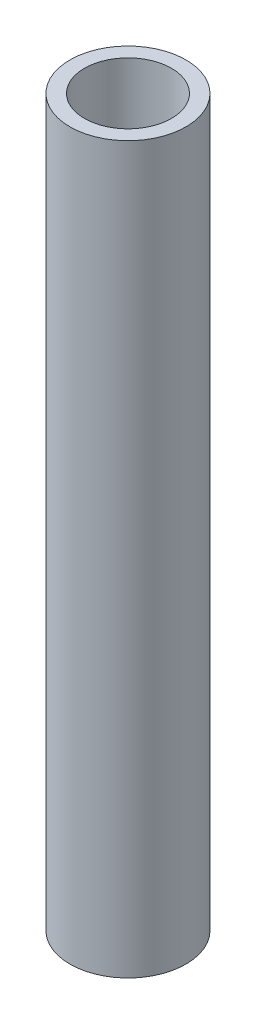
SolidWorks part; units mm, degrees
ref_plane "前基準面" through (0, 0, 0) normal (0, 0, 1) x (1, 0, 0)
ref_plane "上基準面" through (0, 0, 0) normal (0, 1, 0) x (1, 0, 0)
ref_plane "右基準面" through (0, 0, 0) normal (1, 0, 0) x (0, 0, -1)
sketch "草圖2" plane through (0, 0, 0) normal (0, 1, 0) x (1, 0, 0)
  circle A0 centre (0, 0) radius 20
  dimension "D1" = 40
extrude "填料-伸長1" add sketch "草圖2" along normal blind 250
sketch "草圖3" plane through (0, 0, 0) normal (0, -1, 0) x (1, 0, 0)
  circle A0 centre (0, 0) radius 15
  dimension "D1" = 30
extrude "除料-伸長1" cut sketch "草圖3" against normal blind 250 contours A0
